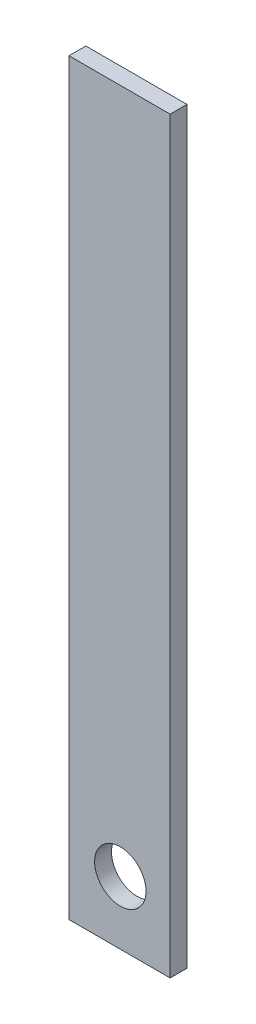
SolidWorks part; units mm, degrees
ref_plane "Front Plane" through (0, 0, 0) normal (0, 0, 1) x (1, 0, 0)
ref_plane "Top Plane" through (0, 0, 0) normal (0, 1, 0) x (1, 0, 0)
ref_plane "Right Plane" through (0, 0, 0) normal (1, 0, 0) x (0, 0, -1)
sketch "Sketch2" plane through (0, 0, 0) normal (0, 0, 1) x (-1, 0, 0)
  line L0 (91.1198, 273.8429) -> (103.1198, 273.8429)
  line L2 (103.1198, 273.8429) -> (103.1198, 185.0788)
  line L4 (103.1198, 185.0788) -> (91.1198, 185.0788)
  line L5 (91.1198, 185.0788) -> (91.1198, 273.8429)
  circle A0 centre (97.0336, 266.3657) radius 3.05
  dimension "D1" = 12
extrude "Boss-Extrude1" add sketch "Sketch2" along normal blind 2 contours A0 | L2 L4 L5 L0
